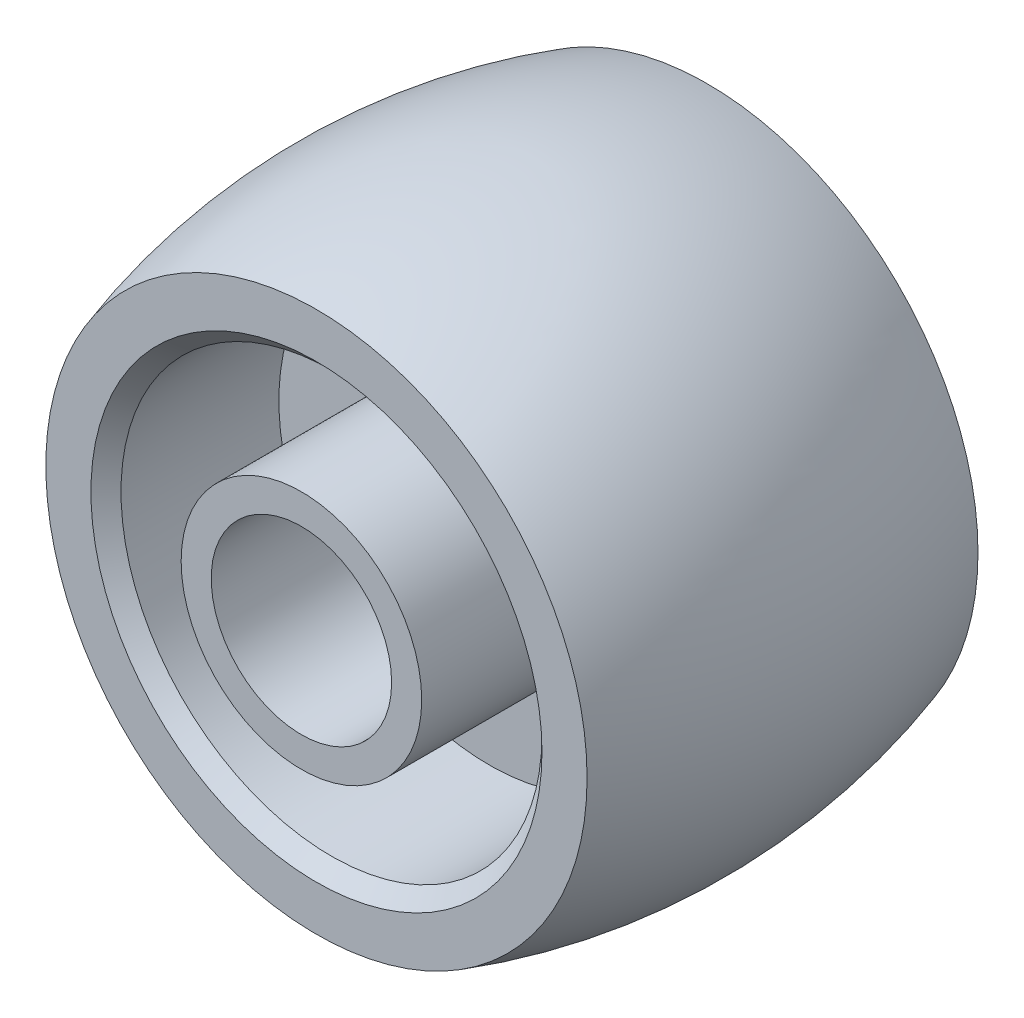
SolidWorks part; units mm, degrees
material "Nylon 101"
ref_plane "Plan de face" through (0, 0, 0) normal (0, 0, 1) x (1, 0, 0)
ref_plane "Plan de dessus" through (0, 0, 0) normal (0, 1, 0) x (1, 0, 0)
ref_plane "Plan de droite" through (0, 0, 0) normal (1, 0, 0) x (0, 0, -1)
sketch "Esquisse1" plane through (0, 0, 0) normal (1, 0, 0) x (0, 0, -1)
  line L0 (-4.7147, 0) -> (4.792, 0) construction
  line L1 (7, 3) -> (-7, 3)
  line L2 (-7, 3) -> (-7, 4)
  line L3 (-7, 4) -> (-0.75, 4)
  line L4 (-0.75, 4) -> (-0.75, 7)
  line L5 (-0.75, 7) -> (-6, 7)
  line L6 (-6.5, 7.5) -> (-6.5, 9)
  line L7 (0, -13.8929) -> (0, 13.236) construction
  line L8 (6.5, 7.5) -> (6.5, 9)
  line L9 (0.75, 7) -> (6, 7)
  line L10 (0.75, 4) -> (0.75, 7)
  line L11 (7, 4) -> (0.75, 4)
  line L12 (7, 3) -> (7, 4)
  line L13 (-6, 7) -> (-6.5, 7.5)
  line L14 (6, 7) -> (6.5, 7.5)
  arc A0 (6.5, 9) -> (-6.5, 9) centre (0, -11.625) ccw
  point P9 (-6.5, 7)
  point P14 (-0.75, 5.5)
  point P16 (6.5, 7)
  point P22 (0, 3)
  point P26 (0, 10)
  dimension "D8" = 10
  dimension "D1" = 3
  dimension "D2" = 4
  dimension "D3" = 7
  dimension "D4" = 2
  dimension "D5" = 6.5
  dimension "D6" = 7
  dimension "D7" = 1.5
revolve "Révolution1" add sketch "Esquisse1" angle 360 about L0
